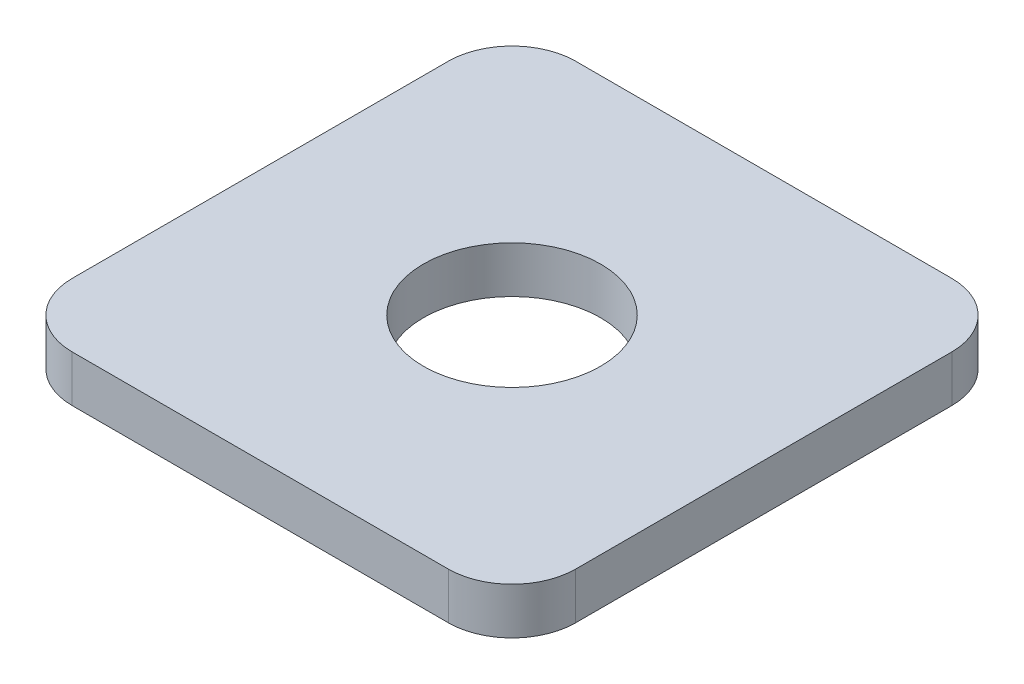
SolidWorks part; units mm, degrees
ref_plane "Front Plane" through (0, 0, 0) normal (0, 0, 1) x (1, 0, 0)
ref_plane "Top Plane" through (0, 0, 0) normal (0, 1, 0) x (1, 0, 0)
ref_plane "Right Plane" through (0, 0, 0) normal (1, 0, 0) x (0, 0, -1)
sketch "Sketch1" plane through (0, 0, 0) normal (0, 1, 0) x (1, 0, 0)
  line L1 (-19.75, 19.75) -> (19.75, 19.75)
  line L2 (-19.75, 19.75) -> (-19.75, -19.75)
  line L3 (-19.75, -19.75) -> (19.75, -19.75)
  line L4 (19.75, 19.75) -> (19.75, -19.75)
  circle A0 centre (0, 0) radius 6.95
  dimension "D1" = 13.9
  dimension "D2" = 39.5
  dimension "D3" = 39.5
  dimension "D4" = 19.75
  dimension "D5" = 19.75
extrude "Boss-Extrude1" add sketch "Sketch1" along normal blind 3.65
fillet "Fillet1" radius 5 4 edges at (19.75, 1.825, 19.75) (-19.75, 1.825, 19.75) (-19.75, 1.825, -19.75) (19.75, 1.825, -19.75)
